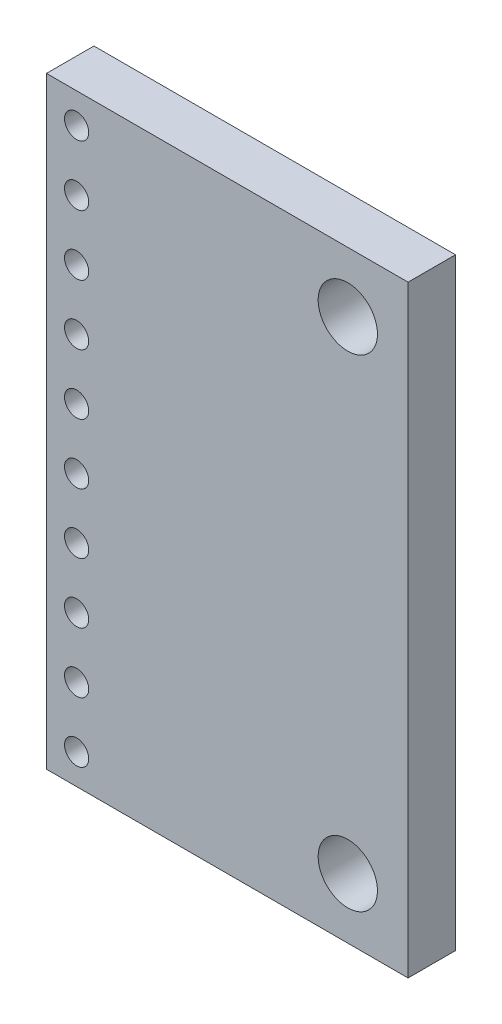
SolidWorks part; units mm, degrees
ref_plane "Front Plane" through (0, 0, 0) normal (0, 0, 1) x (1, 0, 0)
ref_plane "Top Plane" through (0, 0, 0) normal (0, 1, 0) x (1, 0, 0)
ref_plane "Right Plane" through (0, 0, 0) normal (1, 0, 0) x (0, 0, -1)
sketch "Sketch1" plane through (0, 0, 0) normal (0, 0, 1) x (1, 0, 0)
  line L0 (0, 12.7) -> (15.24, 12.7) construction
  line L1 (0, 0) -> (15.24, 0)
  line L2 (0, 0) -> (0, 25.4)
  line L3 (0, 25.4) -> (15.24, 25.4)
  line L4 (15.24, 0) -> (15.24, 25.4)
  circle A0 centre (1.27, 24.13) radius 0.51
  circle A1 centre (1.27, 21.59) radius 0.51
  circle A2 centre (1.27, 19.05) radius 0.51
  circle A3 centre (1.27, 16.51) radius 0.51
  circle A4 centre (1.27, 13.97) radius 0.51
  circle A5 centre (1.27, 11.43) radius 0.51
  circle A6 centre (1.27, 8.89) radius 0.51
  circle A7 centre (1.27, 6.35) radius 0.51
  circle A8 centre (1.27, 3.81) radius 0.51
  circle A9 centre (1.27, 1.27) radius 0.51
  circle A10 centre (12.7, 22.86) radius 1.25
  circle A11 centre (12.7, 2.54) radius 1.25
  dimension "D4" = 1.27
  dimension "D5" = 1.02
  dimension "D7" = 2.5
  dimension "D9" = 2.54
  dimension "D1" = 15.24
  dimension "D2" = 25.4
  dimension "D3" = 1.27
  dimension "D8" = 2.54
  dimension "D6" = 10
extrude "Boss-Extrude1" add sketch "Sketch1" along normal blind 2
